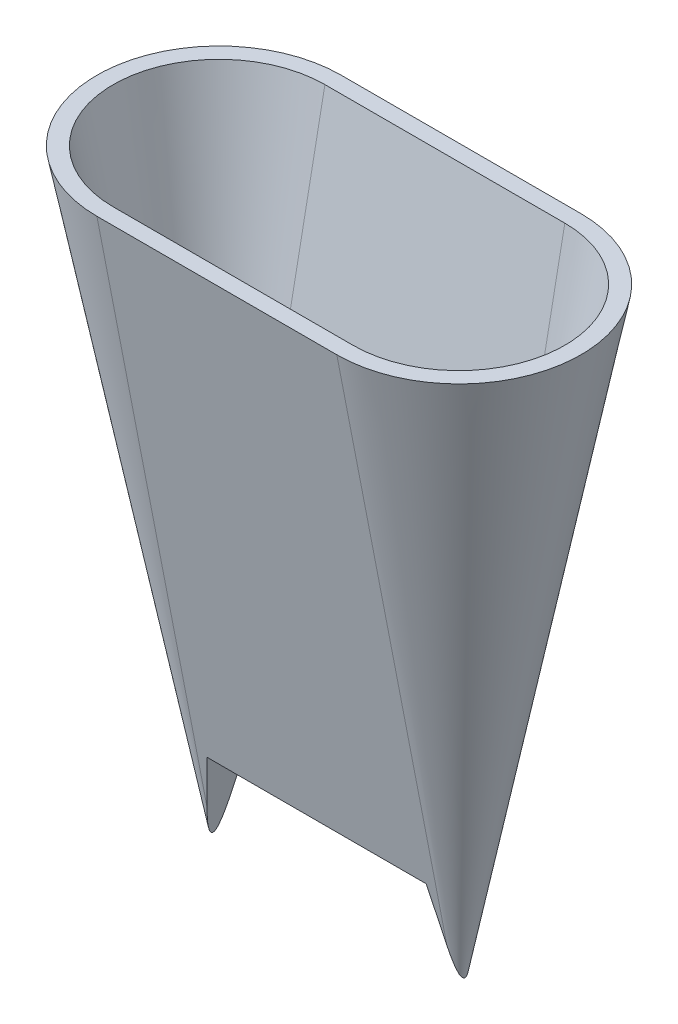
SolidWorks part; units mm, degrees
ref_plane "Front Plane" through (0, 0, 0) normal (0, 0, 1) x (1, 0, 0)
ref_plane "Top Plane" through (0, 0, 0) normal (0, 1, 0) x (1, 0, 0)
ref_plane "Right Plane" through (0, 0, 0) normal (1, 0, 0) x (0, 0, -1)
sketch "Sketch1" plane through (0, 0, 0) normal (0, 1, 0) x (1, 0, 0)
  line L1 (-15, 7.5) -> (15, 7.5)
  line L3 (-15, -7.5) -> (15, -7.5)
  arc A0 (-15, 7.5) -> (-15, -7.5) centre (-15, 0) ccw
  arc A1 (15, 7.5) -> (15, -7.5) centre (15, 0) cw
  point P4 (0, 7.5)
  dimension "D1" = 15
  dimension "D2" = 30
extrude "Boss-Extrude1" add sketch "Sketch1" against normal blind 18 draft 11 and the other way blind 40 draft 11
shell "Shell1" thickness 2
sketch "Sketch2" plane through (0, -18, 0) normal (0, -1, 0) x (1, 0, 0)
  line L0 (15, -15.2752) -> (15, -4.0012) construction
  line L3 (-15, 4.0012) -> (15, 4.0012)
  line L4 (15, -4.0012) -> (-15, -4.0012)
  line L10 (-12.5, 1.6) -> (-12.5, -1.6)
  line L11 (12.5, 1.6) -> (12.5, -1.6)
  line L12 (-12.5, 1.6) -> (12.5, 1.6)
  line L13 (-12.5, -1.6) -> (12.5, -1.6)
  arc A0 (-15, 4.0012) -> (-15, -4.0012) centre (-15, 0) ccw
  arc A1 (15, 4.0012) -> (15, -4.0012) centre (15, 0) cw
  arc A2 (15, -4.0012) -> (15, 4.0012) centre (15, 0) ccw construction
  point P17 (-15, 1.1231)
  point P19 (0, 0)
  point P22 (15.1438, -0.9566)
  point P23 (15.246, 0.9186)
  point P25 (0, 0)
  point P26 (0, 0)
  point P27 (-15, 1.5663)
  point P28 (0, 0)
  point P29 (-12.5, 0)
  point P30 (0, 1.6)
  dimension "D1" = 3.2
  dimension "D2" = 25
extrude "Boss-Extrude2" add sketch "Sketch2" along normal blind 20 draft 11
